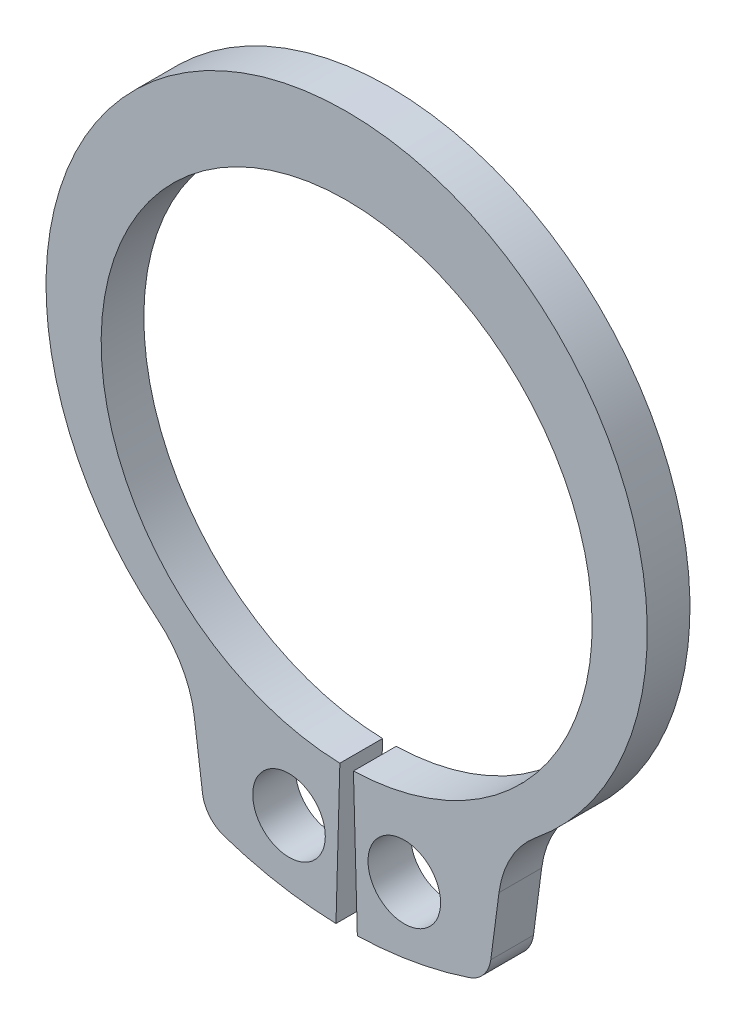
SolidWorks part; units mm, degrees
ref_plane "Plane1" through (0, 0, 0) normal (0, 0, 1) x (1, 0, 0)
ref_plane "Plane2" through (0, 0, 0) normal (0, 1, 0) x (1, 0, 0)
ref_plane "Plane3" through (0, 0, 0) normal (1, 0, 0) x (0, 0, -1)
sketch "Clipboard" plane through (0, 0, 0) normal (0, 0, 1) x (1, 0, 0)
  line L0 (0, 0) -> (1.8, 0)
  line L1 (0, 0) -> (0, 0.9)
  line L2 (0, 0) -> (0, -3.3)
  circle A0 centre (0, 0) radius 0.85
  circle A1 centre (0, 0) radius 6
  dimension "HoleDia" = 1.7
sketch "BodySke" plane through (0, 0, 0) normal (0, 0, 1) x (1, 0, 0)
  line L0 (-1.5431, 0) -> (1.5431, 0) construction
  line L1 (0, 0) -> (0, 7.55) construction
  line L2 (0.1588, -5.7478) -> (0.25, -9.0465)
  line L3 (-0.1588, -5.7478) -> (-0.25, -9.0465)
  line L4 (0, 0) -> (5.9454, -6.8231) construction
  line L5 (0, 0) -> (-5.9454, -6.8231) construction
  line L7 (3.5679, -6.5101) -> (3.3758, -7.9695)
  line L8 (-3.5679, -6.5101) -> (-3.3758, -7.9695)
  circle A0 centre (0, 0) radius 5.75 construction
  arc A1 (0.1588, -5.7478) -> (-0.1588, -5.7478) centre (0, 0) ccw
  arc A2 (4.3687, -5.0137) -> (-4.3687, -5.0137) centre (0, 0.5086) ccw construction
  arc A3 (0.25, -9.0465) -> (2.8701, -8.5828) centre (0, 0) ccw
  arc A4 (4.435, -4.9605) -> (3.5679, -6.5101) centre (5.9454, -6.8231) ccw
  arc A5 (-3.5679, -6.5101) -> (-4.435, -4.9605) centre (-5.9454, -6.8231) ccw
  arc A6 (-2.8701, -8.5828) -> (-0.25, -9.0465) centre (0, 0) ccw
  arc A7 (4.435, -4.9605) -> (-4.435, -4.9605) centre (0, 0.5086) ccw
  arc A8 (-3.5516, -6.6341) -> (3.5516, -6.6341) centre (0, 0) ccw construction
  circle A9 centre (1.35, -7.4029) radius 0.85
  circle A10 centre (-1.35, -7.4029) radius 0.85
  arc A11 (3.3758, -7.9695) -> (2.8701, -8.5828) centre (2.6322, -7.8716) cw
  arc A12 (-3.3758, -7.9695) -> (-2.8701, -8.5828) centre (-2.6322, -7.8716) ccw
  point P28 (3.3164, -8.4204)
  point P31 (-3.3164, -8.4204)
  dimension "HoleDia" = 1.7
  dimension "D3" = 0.75
  dimension "D2" = 15
extrude "Body" add sketch "BodySke" against normal blind 1
sketch "NotSke" plane through (0, 0, 0) normal (0, 0, 1) x (1, 0, 0)
  line L0 (1.35, -6.5529) -> (1.35, -8.2529)
  line L1 (1.35, -8.2529) -> (-1.35, -8.2529)
  line L2 (-1.35, -8.2529) -> (-1.35, -6.5529)
  line L3 (-1.35, -6.5529) -> (1.35, -6.5529)
  circle A0 centre (1.35, -7.4029) radius 0.85 construction
  circle A1 centre (-1.35, -7.4029) radius 0.85 construction
extrude "Notch" [suppressed] cut sketch "NotSke" against normal through all
sketch "UnlSke" plane through (0, 0, 0) normal (0, 0, 1) x (1, 0, 0)
  line L0 (-2.6189, -8.6628) -> (-1.6639, -5.504)
  line L1 (2.6189, -8.6628) -> (1.6639, -5.504)
  arc A0 (1.6639, -5.504) -> (-1.6639, -5.504) centre (0, 0) ccw
  arc A1 (2.6189, -8.6628) -> (-2.6189, -8.6628) centre (0, 0) ccw
  arc A2 (0.25, -9.0465) -> (2.8701, -8.5828) centre (0, 0) ccw construction
  arc A3 (0.1588, -5.7478) -> (-0.1588, -5.7478) centre (0, 0) ccw construction
  circle A4 centre (-1.35, -7.4029) radius 0.85 construction
  circle A5 centre (1.35, -7.4029) radius 0.85 construction
extrude "Unlug" [suppressed] add sketch "UnlSke" against normal through all
equation "' \"ShaftDia@Clipboard\" = 3"
equation "' \"Thickness@Body\" = 0.4"
equation "' \"GrooveDia@BodySke\" = 2.8"
equation "' \"LugSection@Clipboard\" = 1.9"
equation "' \"LargeSection@Clipboard\" = 0.8"
equation "' \"HoleDia@Clipboard\" = 1.0"
equation "' \"ShaftDia@Clipboard\" = 10"
equation "' \"Thickness@Body\" = 1.0"
equation "' \"GrooveDia@BodySke\" = 9.6"
equation "' \"LugSection@Clipboard\" = 3.3"
equation "' \"LargeSection@Clipboard\" = 1.8"
equation "' \"HoleDia@Clipboard\" = 1.5"
equation "\"SmallSection@Clipboard\" = \"LargeSection@Clipboard\" * 0.5"
equation "\"Gap@BodySke\" =  \"Thickness@Body\" / 2"
equation "\"LargeRad@BodySke\" =  \"GrooveDia@BodySke\" / 2 +  \"LargeSection@Clipboard\""
equation "\"SmallRad@BodySke\" =  \"GrooveDia@BodySke\" / 2 +  \"SmallSection@Clipboard\""
equation "\"LugRad@BodySke\" = \"GrooveDia@BodySke\" / 2 + \"LugSection@Clipboard\""
equation "\"HoleOffsetRad@BodySke\" = (  \"ShaftDia@Clipboard\" / 2 + \"LugRad@BodySke\" ) / 2"
equation "\"HoleSpacing@BodySke\" = \"Gap@BodySke\"  * 2 +  \"HoleDia@Clipboard\""
equation "\"HoleDia@BodySke\" =  \"HoleDia@Clipboard\""
equation "\"SmallAngle@BodySke\" = atn(\"HoleSpacing@BodySke\" / 2 / sqr(\"HoleOffsetRad@BodySke\"  * \"HoleOffsetRad@BodySke\" - (\"HoleSpacing@BodySke\" / 2) * (\"HoleSpacing@BodySke\" / 2) ))  * 7 *  (\"LargeRad@BodySke\" / \"SmallRad@BodySke\")* ( 180 / 3.141593)"
